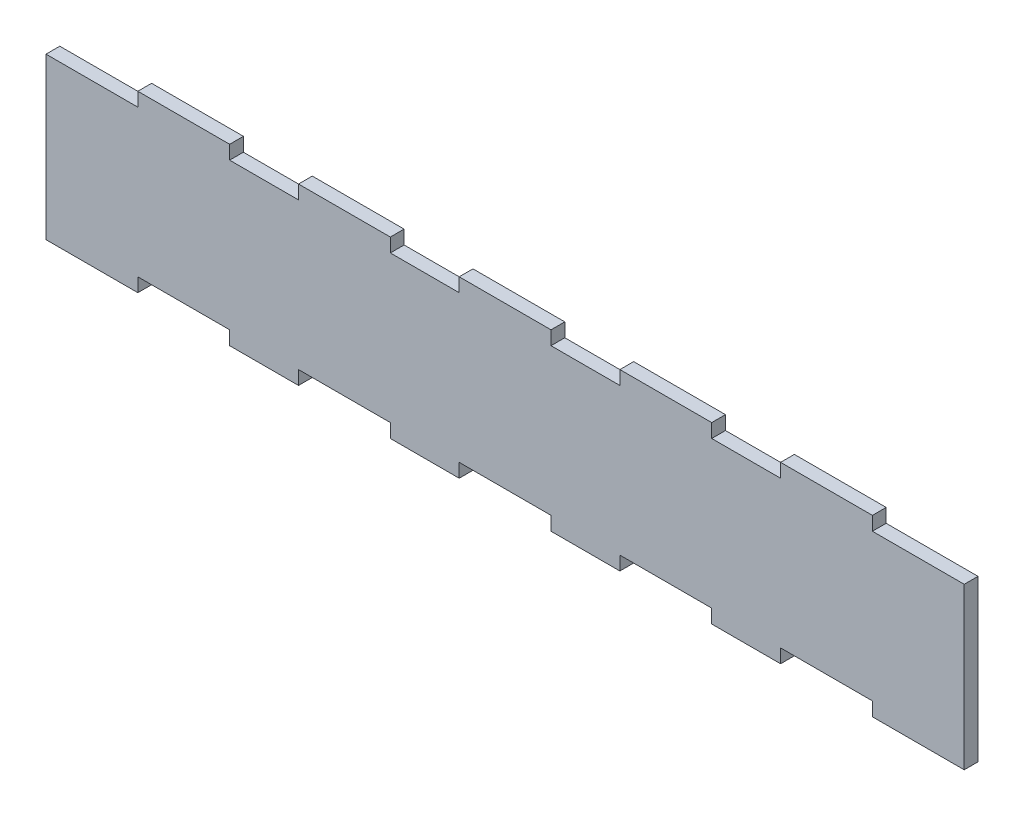
SolidWorks part; units mm, degrees
ref_plane "Front Plane" through (0, 0, 0) normal (0, 0, 1) x (1, 0, 0)
ref_plane "Top Plane" through (0, 0, 0) normal (0, 1, 0) x (1, 0, 0)
ref_plane "Right Plane" through (0, 0, 0) normal (1, 0, 0) x (0, 0, -1)
sketch "Sketch1" plane through (0, 0, 0) normal (0, 0, -1) x (1, 0, 0)
  line L0 (40, 0) -> (55, 0)
  line L1 (0, 0) -> (20, 0)
  line L2 (0, 0) -> (0, 35)
  line L3 (0, 35) -> (20, 35)
  line L4 (200, 0) -> (200, 35)
  line L5 (0, 0) -> (200, 35) construction
  line L6 (0, 35) -> (200, 0) construction
  line L7 (55, -3) -> (75, -3)
  line L8 (20, 0) -> (20, -3)
  line L9 (20, -3) -> (40, -3)
  line L10 (40, 0) -> (40, -3)
  line L11 (75, 0) -> (75, -3)
  line L12 (55, 0) -> (55, -3)
  line L13 (90, -3) -> (110, -3)
  line L14 (110, 0) -> (110, -3)
  line L15 (90, 0) -> (90, -3)
  line L16 (125, -3) -> (145, -3)
  line L17 (145, 0) -> (145, -3)
  line L18 (125, 0) -> (125, -3)
  line L19 (160, -3) -> (180, -3)
  line L20 (180, 0) -> (180, -3)
  line L21 (160, 0) -> (160, -3)
  line L22 (75, 0) -> (90, 0)
  line L23 (110, 0) -> (125, 0)
  line L24 (145, 0) -> (160, 0)
  line L25 (180, 0) -> (200, 0)
  line L26 (40, 35) -> (55, 35)
  line L27 (55, 32) -> (75, 32)
  line L28 (20, 35) -> (20, 32)
  line L29 (20, 32) -> (40, 32)
  line L30 (40, 35) -> (40, 32)
  line L31 (55, 35) -> (55, 32)
  line L32 (75, 35) -> (75, 32)
  line L33 (90, 32) -> (110, 32)
  line L34 (90, 35) -> (90, 32)
  line L35 (110, 35) -> (110, 32)
  line L36 (125, 32) -> (145, 32)
  line L37 (125, 35) -> (125, 32)
  line L38 (145, 35) -> (145, 32)
  line L39 (160, 32) -> (180, 32)
  line L40 (160, 35) -> (160, 32)
  line L41 (180, 35) -> (180, 32)
  line L42 (75, 35) -> (90, 35)
  line L43 (110, 35) -> (125, 35)
  line L44 (145, 35) -> (160, 35)
  line L45 (180, 35) -> (200, 35)
  point P4 (100, 17.5)
  point P10 (25.3866, 2.1907)
  dimension "D1" = 20
  dimension "D2" = 20
  dimension "D3" = 3
  dimension "D4" = 200
  dimension "D5" = 35
  dimension "D7" = 15
  dimension "D6" = 5
  dimension "D8" = 5
extrude "Boss-Extrude1" add sketch "Sketch1" along normal blind 3 contours L3 L28 L29 L30 L26 L31 L27 L32 L42 L34 L33 L35 L43 L37 L36 L38 L44 L40 L39 L41 L45 L4 L25 L20 L19 L21 L24 L17 L16 L18 L23 L14 L13 L15 L22 L11 L7 L12 L0 L10 L9 L8 L1 L2
